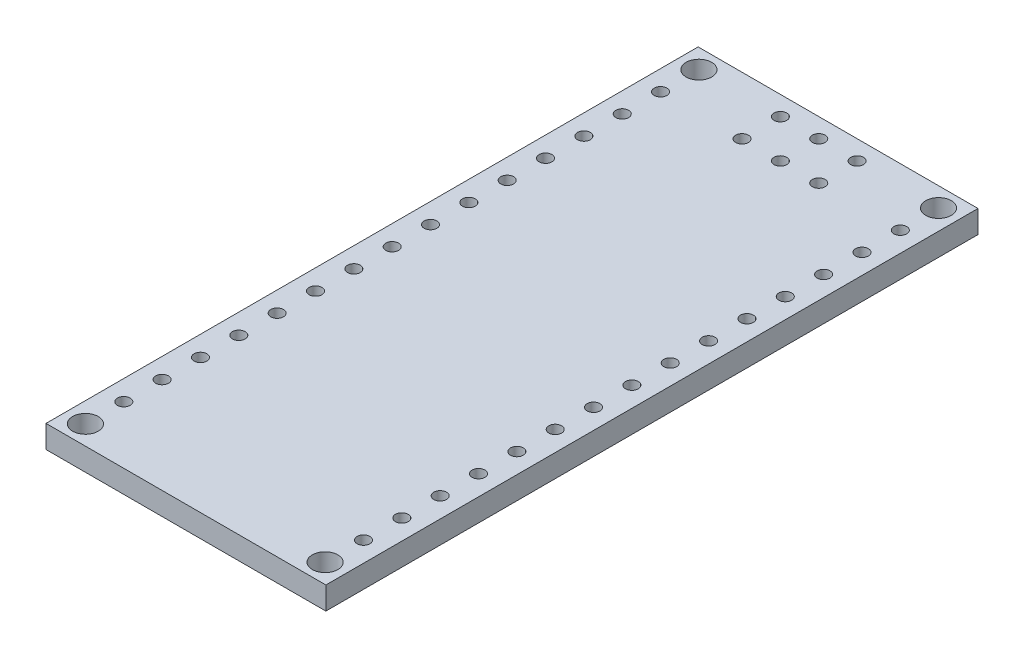
SolidWorks part; units mm, degrees
material "Processing Board, Complex"
ref_plane "Front Plane" through (0, 0, 0) normal (0, 0, 1) x (1, 0, 0)
ref_plane "Top Plane" through (0, 0, 0) normal (0, 1, 0) x (1, 0, 0)
ref_plane "Right Plane" through (0, 0, 0) normal (1, 0, 0) x (0, 0, -1)
sketch "Sketch1" plane through (0, 0, 0) normal (0, 1, 0) x (1, 0, 0)
  line L1 (-9.27, -21.6) -> (9.27, -21.6)
  line L2 (-9.27, -21.6) -> (-9.27, 21.6)
  line L3 (-9.27, 21.6) -> (9.27, 21.6)
  line L4 (9.27, -21.6) -> (9.27, 21.6)
  line L5 (-9.27, -21.6) -> (9.27, 21.6) construction
  line L6 (-9.27, 21.6) -> (9.27, -21.6) construction
  point P0 (0, 0)
  dimension "D1" = 43.2
  dimension "D2" = 18.54
extrude "Boss-Extrude1" add sketch "Sketch1" along normal blind 1.5
sketch "Sketch2" plane through (0, 1.5, 0) normal (0, 1, 0) x (1, 0, 0)
  line L0 (-7.9375, -17.78) -> (-7.9375, -15.24) construction
  line L1 (-7.9375, 20.32) -> (7.9375, 20.32) construction
  line L2 (-7.9375, 20.32) -> (-7.9375, -20.32) construction
  line L3 (-7.9375, -20.32) -> (7.9375, -20.32) construction
  line L4 (7.9375, 20.32) -> (7.9375, -20.32) construction
  line L5 (-7.9375, 20.32) -> (7.9375, -20.32) construction
  line L6 (-7.9375, -20.32) -> (7.9375, 20.32) construction
  line L7 (-7.9375, -17.78) -> (7.9425, -17.78) construction
  line L8 (-2.54, 20.32) -> (-2.54, 17.78) construction
  circle A0 centre (7.9375, 20.32) radius 0.8467
  circle A1 centre (7.9375, -20.32) radius 0.8467
  circle A2 centre (-7.9375, -20.32) radius 0.8467
  circle A3 centre (-7.9375, 20.32) radius 0.8467
  circle A4 centre (-7.9375, -17.78) radius 0.4233
  circle A5 centre (-7.9375, -15.24) radius 0.4233
  circle A6 centre (-7.9375, -12.7) radius 0.4233
  circle A7 centre (-7.9375, -10.16) radius 0.4233
  circle A8 centre (-7.9375, -7.62) radius 0.4233
  circle A9 centre (-7.9375, -5.08) radius 0.4233
  circle A10 centre (-7.9375, -2.54) radius 0.4233
  circle A11 centre (-7.9375, 0) radius 0.4233
  circle A12 centre (-7.9375, 2.54) radius 0.4233
  circle A13 centre (-7.9375, 5.08) radius 0.4233
  circle A14 centre (-7.9375, 7.62) radius 0.4233
  circle A15 centre (-7.9375, 10.16) radius 0.4233
  circle A16 centre (-7.9375, 12.7) radius 0.4233
  circle A17 centre (-7.9375, 15.24) radius 0.4233
  circle A18 centre (-7.9375, 17.78) radius 0.4233
  circle A19 centre (7.9425, -15.24) radius 0.4233
  circle A20 centre (7.9425, -12.7) radius 0.4233
  circle A21 centre (7.9425, -10.16) radius 0.4233
  circle A22 centre (7.9425, -7.62) radius 0.4233
  circle A23 centre (7.9425, -5.08) radius 0.4233
  circle A24 centre (7.9425, -2.54) radius 0.4233
  circle A25 centre (7.9425, 0) radius 0.4233
  circle A26 centre (7.9425, 2.54) radius 0.4233
  circle A27 centre (7.9425, 5.08) radius 0.4233
  circle A28 centre (7.9425, 7.62) radius 0.4233
  circle A29 centre (7.9425, 10.16) radius 0.4233
  circle A30 centre (7.9425, 12.7) radius 0.4233
  circle A31 centre (7.9425, 15.24) radius 0.4233
  circle A32 centre (7.9425, 17.78) radius 0.4233
  circle A33 centre (7.9425, -17.78) radius 0.4233
  circle A34 centre (0, 20.32) radius 0.4233
  circle A35 centre (-2.54, 20.32) radius 0.4233
  circle A36 centre (2.54, 20.32) radius 0.4233
  circle A37 centre (-2.54, 17.78) radius 0.4233
  circle A38 centre (0, 17.78) radius 0.4233
  circle A39 centre (2.54, 17.78) radius 0.4233
  point P0 (0, 0)
  dimension "D1" = 40.64
  dimension "D3" = 1.6933
  dimension "D4" = 2.54
  dimension "D5" = 0.8467
  dimension "D6" = 15
  dimension "D10" = 2.54
  dimension "D2" = 15.875
  dimension "D8" = 2.54
  dimension "D9" = 15.88
  dimension "D11" = 2.54
  dimension "D13" = 2.54
  dimension "D7" = 2
  dimension "D12" = 2
extrude "Cut-Extrude1" cut sketch "Sketch2" against normal through all
